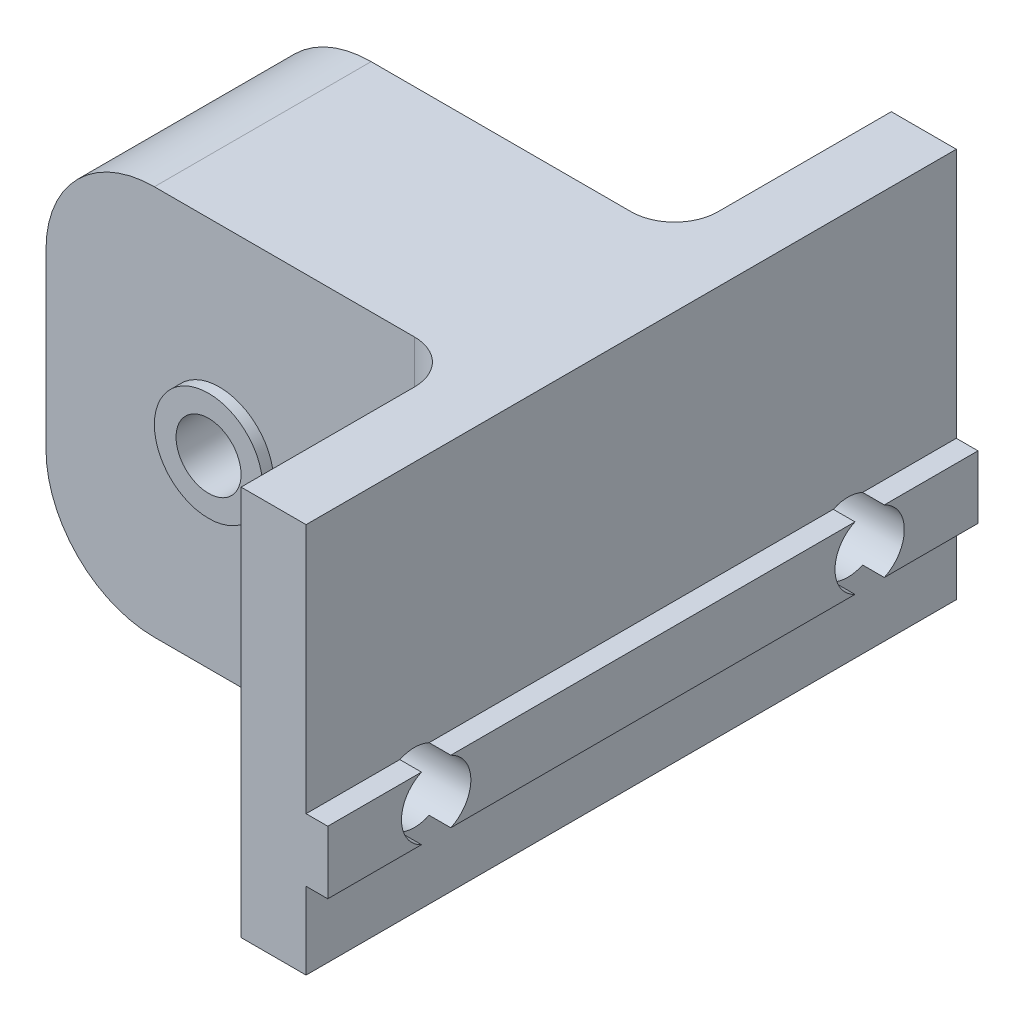
SolidWorks part; units mm, degrees
ref_plane "Front Plane" through (0, 0, 0) normal (0, 0, 1) x (1, 0, 0)
ref_plane "Top Plane" through (0, 0, 0) normal (0, 1, 0) x (1, 0, 0)
ref_plane "Right Plane" through (0, 0, 0) normal (1, 0, 0) x (0, 0, -1)
sketch "Esquisse1" plane through (0, 0, 0) normal (0, 0, 1) x (1, 0, 0)
  line L0 (-11, 13) -> (-11, -5)
  line L1 (-11, 13) -> (11, 13)
  line L2 (11, 13) -> (11, 1.45)
  line L3 (11, 1.45) -> (12, 1.45)
  line L4 (12, 1.45) -> (12, -1.45)
  line L5 (12, -1.45) -> (11, -1.45)
  line L6 (11, -1.45) -> (11, -5)
  line L7 (11, -5) -> (-11, -5)
  point P8 (12, 0)
  point P10 (0, -5)
  dimension "D1" = 2.9
  dimension "D2" = 18
  dimension "D3" = 1
  dimension "D4" = 22
  dimension "D5" = 3.55
extrude "Main Extrusion" add sketch "Esquisse1" along normal blind 30
sketch "Esquisse2" plane through (0, 13, 0) normal (0, 1, 0) x (1, 0, 0)
  line L0 (-11, -30) -> (-11, 0) construction
  line L1 (-11, 0) -> (8, 0)
  line L2 (-11, 0) -> (-11, -10)
  line L3 (-11, -10) -> (8, -10)
  line L4 (8, 0) -> (8, -10)
  line L5 (11, -30) -> (-11, -30) construction
  line L6 (-11, -30) -> (8, -30)
  line L7 (-11, -30) -> (-11, -20)
  line L8 (-11, -20) -> (8, -20)
  line L9 (8, -30) -> (8, -20)
  line L10 (11, 0) -> (-11, 0) construction
  line L12 (11, -30) -> (11, 0) construction
  dimension "D1" = 3
  dimension "D2" = 10
extrude "External Hole" cut sketch "Esquisse2" against normal through all
sketch "Esquisse3" plane through (8, 0, 0) normal (-1, 0, 0) x (0, 0, 1)
  line L1 (30, -5) -> (30, 13) construction
  line L4 (0, -1.45) -> (0, 1.45) construction
  line L5 (30, 1.45) -> (30, 13) construction
  circle A0 centre (5, 0) radius 1.6
  circle A1 centre (25, 0) radius 1.6
  point P5 (0, 0)
  dimension "D1" = 3.2
  dimension "D2" = 5
  dimension "D3" = 5
extrude "MakerBeamFixingHole" cut sketch "Esquisse3" against normal through all
sketch "Esquisse4" plane through (0, 0, 20) normal (0, 0, 1) x (1, 0, 0)
  line L0 (8, -5) -> (8, 13) construction
  line L1 (-11, -5) -> (-11, 13) construction
  circle A0 centre (-3, 4) radius 1.5
  point P7 (-11, 4)
  dimension "D1" = 3
  dimension "D2" = 11
extrude "HoleLinkWithCodersSupport" cut sketch "Esquisse4" against normal through all
fillet "Congé2" radius 2 2 edges at (8, 4, 20) (8, 4, 10)
fillet "Congé3" radius 5 2 edges at (-11, -5, 15) (-11, 13, 15)
sketch "Esquisse6" plane through (0, 0, 10) normal (0, 0, -1) x (-1, 0, 0)
  circle A0 centre (3, 4) radius 1.5
  circle A1 centre (3, 4) radius 1.5 construction
  circle A2 centre (3, 4) radius 2.5
  dimension "D1" = 5
extrude "Boss.-Extru.1" add sketch "Esquisse6" along normal blind 0.5
sketch "Esquisse7" plane through (0, 0, 20) normal (0, 0, 1) x (1, 0, 0)
  circle A0 centre (-3, 4) radius 1.5
  circle A1 centre (-3, 4) radius 1.5 construction
  circle A2 centre (-3, 4) radius 2.5
  dimension "D1" = 5
extrude "Boss.-Extru.2" add sketch "Esquisse7" along normal blind 0.5
